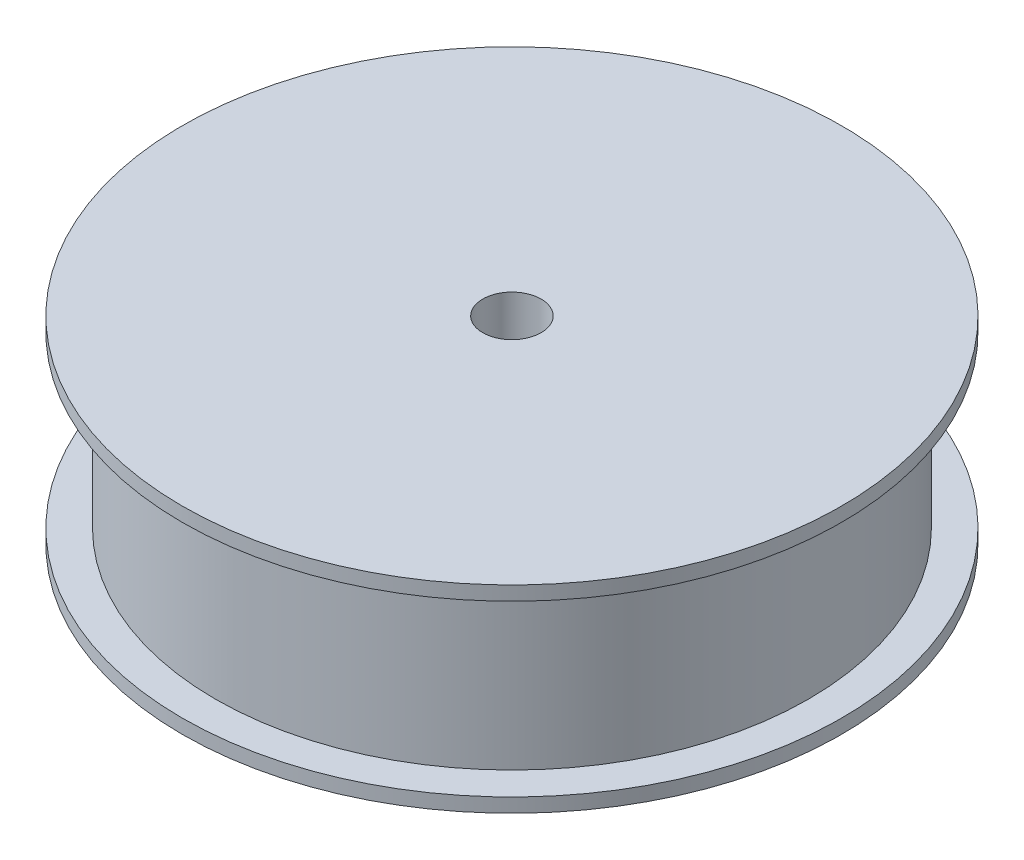
SolidWorks part; units mm, degrees
ref_plane "Front Plane" through (0, 0, 0) normal (0, 0, 1) x (1, 0, 0)
ref_plane "Top Plane" through (0, 0, 0) normal (0, 1, 0) x (1, 0, 0)
ref_plane "Right Plane" through (0, 0, 0) normal (1, 0, 0) x (0, 0, -1)
sketch "Sketch1" plane through (0, 0, 0) normal (0, 1, 0) x (1, 0, 0)
  circle A0 centre (0, 0) radius 35
  dimension "D1" = 70
extrude "Boss-Extrude1" add sketch "Sketch1" along normal blind 1.5
sketch "Sketch2" plane through (0, 1.5, 0) normal (0, 1, 0) x (1, 0, 0)
  circle A0 centre (0, 0) radius 31.5
  dimension "D1" = 63
extrude "Boss-Extrude2" add sketch "Sketch2" along normal blind 18
sketch "Sketch3" plane through (0, 19.5, 0) normal (0, 1, 0) x (1, 0, 0)
  circle A0 centre (0, 0) radius 35
  dimension "D1" = 70
extrude "Boss-Extrude3" add sketch "Sketch3" along normal blind 1.5
sketch "Sketch4" plane through (0, 21, 0) normal (0, 1, 0) x (1, 0, 0)
  circle A0 centre (0, 0) radius 3.1
  dimension "D1" = 6.2
extrude "Cut-Extrude1" cut sketch "Sketch4" against normal through all
